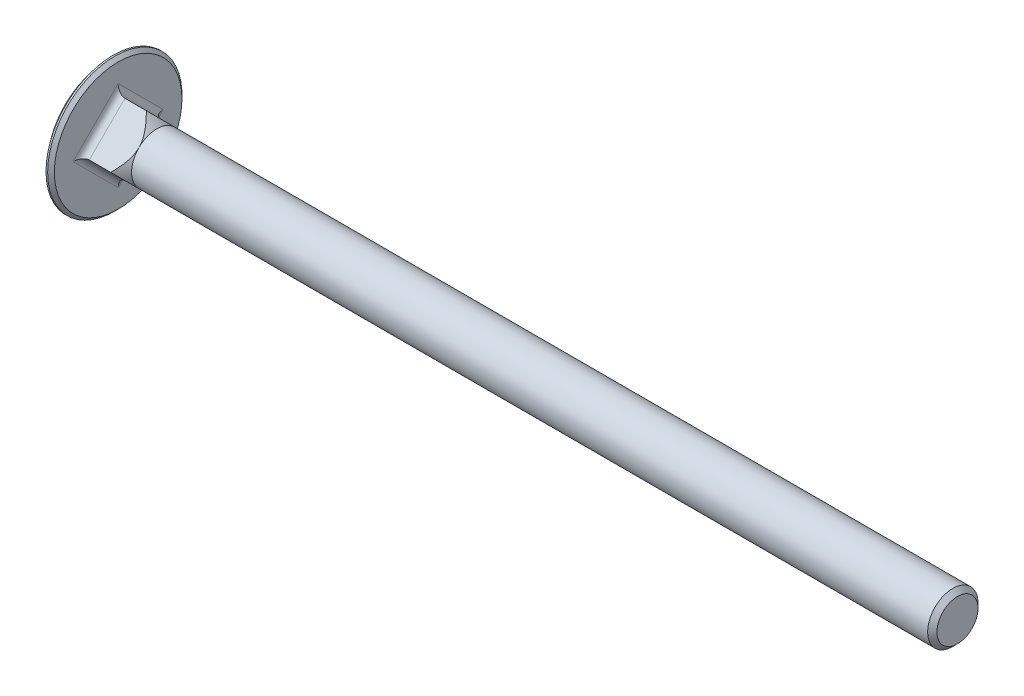
SolidWorks part; units mm, degrees
revolve "Base-Revolve" add sketch "BodySke" angle 360 about L6
sketch "BodySke" plane through (0, 0, 0) normal (0, 0, 1) x (1, 0, 0)
  line L1 (3.0024, 8) -> (3.6, 8)
  line L2 (3.6, 8) -> (3.6, 3)
  line L3 (3.6, 3) -> (103.0455, 3)
  line L4 (103.6, 2.4455) -> (103.6, 0)
  line L5 (103.6, 0) -> (0, 0)
  line L6 (-31.75, 0) -> (127, 0) construction
  line L8 (103.6, 2.4455) -> (103.0455, 3)
  line L10 (103.6, -2.4455) -> (103.0455, -3) construction
  line L11 (4.6, 7.799) -> (4.6, 1.449) construction
  line L12 (85.6, 7.799) -> (85.6, 1.449) construction
  line L13 (3.6, 7.799) -> (3.6, 1.449) construction
  arc A0 (3.0024, 8) -> (0, 0) centre (12.1593, 0) ccw
  dimension "Length" = 100
  dimension "Body_ch_ang" = 45
  dimension "Diameter" = 6
  dimension "Minor_dia" = 4.891
  dimension "Advance" = 1
  dimension "Thread_nom" = 18
  dimension "Thread_length" = 100
  dimension "Head_dia" = 16
  dimension "Head_ht" = 3.6
  dimension "D1" = 0.5976
cosmetic thread "ThreadCosmetic" [suppressed] parameters "Thread_length"=18, "Thread_minor"=4.891
ref_plane "Plane1" through (0, 0, 0) normal (0, 0, 1) x (1, 0, 0)
ref_plane "Plane2" through (0, 0, 0) normal (0, 1, 0) x (1, 0, 0)
ref_plane "Plane3" through (0, 0, 0) normal (1, 0, 0) x (0, 0, -1)
sketch "Sketch1" plane through (3.6, 0, 0) normal (1, 0, 0) x (0, 0, -1)
  line L0 (0, 4.2426) -> (4.2426, 0)
  line L1 (4.2426, 0) -> (0, -4.2426)
  line L2 (0, -4.2426) -> (-4.2426, 0)
  line L3 (-4.2426, 0) -> (0, 4.2426)
  circle A0 centre (0, 0) radius 3 construction
  circle A1 centre (0, 0) radius 8 construction
  dimension "D1" = 6
extrude "Boss-Extrude1" add sketch "Sketch1" along normal blind 4.6
sketch "Sketch2" plane through (0, 0, 0) normal (0, 0, 1) x (1, 0, 0)
  line L0 (0, 0) -> (101.6, 0) construction
  line L1 (8.2, 3) -> (13.2, 3)
  line L2 (8.2, 3) -> (2.2, 9)
  line L3 (13.2, 3) -> (13.2, 9)
  line L4 (13.2, 9) -> (2.2, 9)
  dimension "D1" = 6
  dimension "D2" = 8.2
  dimension "D3" = 18
  dimension "D4" = 5
  dimension "D5" = 45
revolve "Cut-Revolve1" cut sketch "Sketch2" angle 360 about L0
fillet "Fillet1" radius 0.8 4 edges at (3.6, 2.1213, -2.1213) (3.6, -2.1213, -2.1213) (3.6, 2.1213, 2.1213) (3.6, -2.1213, 2.1213)
sketch "ThdSchSke" plane through (0, 0, 0) normal (0, 0, 1) x (1, 0, 0)
  line L0 (85.6, -2.4455) -> (85.2117, -3)
  line L1 (85.6, -2.4455) -> (85.9883, -3)
  line L2 (85.9883, -3) -> (85.9883, -3.75)
  line L3 (0, 0) -> (5.1513, 0) construction
  line L5 (85.9883, -3.75) -> (85.2117, -3.75)
  line L6 (85.2117, -3.75) -> (85.2117, -3)
  arc A0 (3.0024, 8) -> (3.0024, -8) centre (12.1593, 0) ccw construction
  dimension "Thread_minor" = 4.891
  dimension "Diameter" = 6
  dimension "Start" = 85.6
revolve "ThreadSchematic" [suppressed] cut sketch "ThdSchSke" angle 360 about L3
pattern_linear "ThdSchPat" [suppressed]
equation "\"Thread_minor@ThreadCosmetic\"  =  \"Minor_dia@BodySke\""
equation "\"Thread_length@ThreadCosmetic\" = ((sgn( (\"Length@BodySke\" - \"Advance@BodySke\" * 3.0) - \"Thread_nom@BodySke\" )-1)*( (\"Length@BodySke\" - \"Advance@BodySke\" * 3.0) - \"Thread_nom@BodySke\" ))/-2+ \"Thread_nom@BodySke\""
equation "\"Thread_minor@ThdSchSke\" = \"Minor_dia@BodySke\""
equation "\"Diameter@ThdSchSke\" = \"Diameter@BodySke\""
equation "\"Overcut@ThdSchSke\" = \"Diameter@BodySke\" * 1.25"
equation "\"Start@ThdSchSke\" = \"Head_ht@BodySke\" + \"Length@BodySke\" - \"Thread_length@ThreadCosmetic\"  '---Non-countersunk---"
equation "\"Num_threads@ThdSchPat\" = int( \"Thread_length@ThreadCosmetic\" / \"Advance@BodySke\" + 0.999 )  + 1"
equation "\"Advance@ThdSchPat\" = \"Thread_length@ThreadCosmetic\" /  (\"Num_threads@ThdSchPat\" - 1) 'relax it"
equation "\"Num_threads@ThdSchPat\" = \"Num_threads@ThdSchPat\" - sgn( \"Num_threads@ThdSchPat\" - 1) '---chamfered tips only---"
equation "\"D1@BodySke\" = \"Head_ht@BodySke\" * .166"
equation "\"D1@Sketch2\" = \"Diameter@BodySke\""
equation "\"D2@Sketch2\" = \"Head_ht@BodySke\" + \"NeckHt@Boss-Extrude1\""
equation "\"D3@Sketch2\" = \"Head_dia@BodySke\" + 2"
equation "\"D1@Sketch1\" = \"Diameter@BodySke\""
